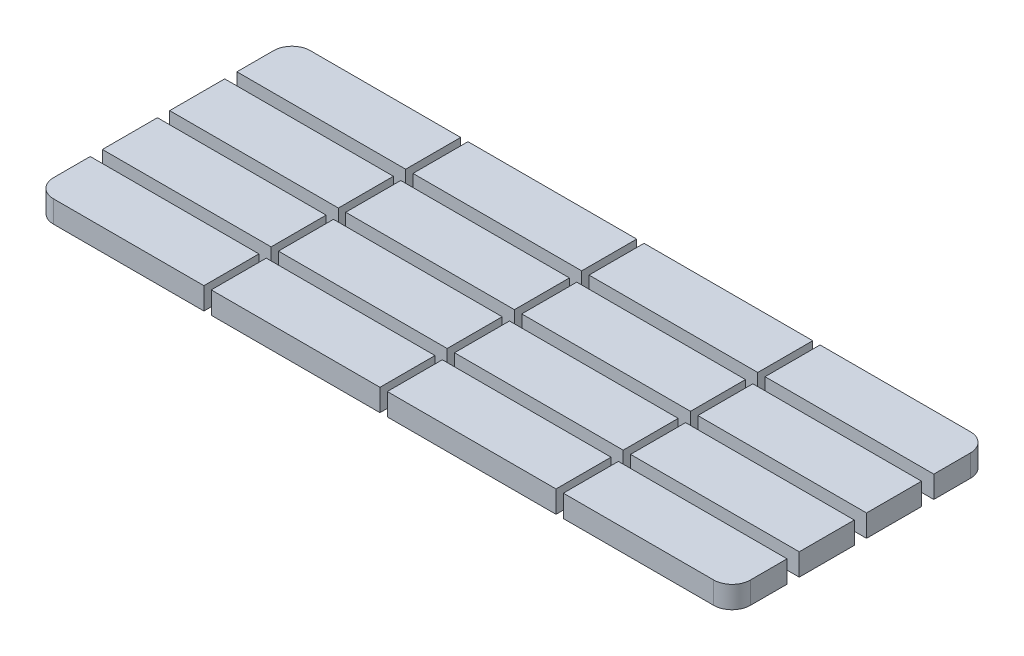
SolidWorks part; units mm, degrees
ref_plane "Front Plane" through (0, 0, 0) normal (0, 0, 1) x (1, 0, 0)
ref_plane "Top Plane" through (0, 0, 0) normal (0, 1, 0) x (1, 0, 0)
ref_plane "Right Plane" through (0, 0, 0) normal (1, 0, 0) x (0, 0, -1)
sketch "Sketch1" plane through (0, 0, 0) normal (0, 1, 0) x (1, 0, 0)
  line L0 (-57.3291, 9.17) -> (-34.3291, 9.17)
  line L1 (-54.8291, 19.17) -> (35.1709, 19.17)
  line L2 (-59.8291, 14.17) -> (-59.8291, -15.83)
  line L3 (-54.8291, -20.83) -> (35.1709, -20.83)
  line L4 (40.1709, 14.17) -> (40.1709, -15.83)
  line L5 (37.6709, 0) -> (14.6709, 0)
  line L6 (-57.3291, -10.83) -> (-34.3291, -10.83)
  line L7 (-33.3291, 16.67) -> (-33.3291, 9.17)
  line L8 (-9.3291, 16.67) -> (-9.3291, 9.17)
  line L9 (14.6709, 16.67) -> (14.6709, 9.17)
  line L10 (-34.3291, 16.67) -> (-34.3291, 9.17)
  line L11 (-54.8291, 16.67) -> (-34.3291, 16.67)
  line L12 (-57.3291, 14.17) -> (-57.3291, 9.17)
  line L13 (-54.8291, -18.33) -> (-34.3291, -18.33)
  line L14 (37.6709, 14.17) -> (37.6709, 9.17)
  line L15 (-10.3291, 16.67) -> (-10.3291, 9.17)
  line L16 (13.6709, 16.67) -> (13.6709, 9.17)
  line L17 (-33.3291, -18.33) -> (-10.3291, -18.33)
  line L18 (-33.3291, -10.83) -> (-10.3291, -10.83)
  line L19 (-34.3291, 0) -> (-57.3291, 0)
  line L20 (-33.3291, 9.17) -> (-10.3291, 9.17)
  line L21 (-33.3291, 16.67) -> (-10.3291, 16.67)
  line L22 (-9.3291, 16.67) -> (13.6709, 16.67)
  line L23 (-9.3291, 9.17) -> (13.6709, 9.17)
  line L24 (-10.3291, 0) -> (-33.3291, 0)
  line L25 (-9.3291, -10.83) -> (13.6709, -10.83)
  line L26 (-9.3291, -18.33) -> (13.6709, -18.33)
  line L27 (14.6709, -18.33) -> (35.1709, -18.33)
  line L28 (14.6709, -10.83) -> (37.6709, -10.83)
  line L29 (13.6709, 0) -> (-9.3291, 0)
  line L30 (14.6709, 16.67) -> (35.1709, 16.67)
  line L31 (14.6709, 9.17) -> (37.6709, 9.17)
  line L32 (-57.3291, 7.5) -> (-34.3291, 7.5)
  line L33 (-57.3291, -1.67) -> (-34.3291, -1.67)
  line L34 (-57.3291, -9.17) -> (-34.3291, -9.17)
  line L35 (-57.3291, 7.5) -> (-57.3291, 0)
  line L36 (-34.3291, 7.5) -> (-34.3291, 0)
  line L37 (-33.3291, 7.5) -> (-33.3291, 0)
  line L38 (-33.3291, 7.5) -> (-10.3291, 7.5)
  line L39 (-57.3291, -1.67) -> (-57.3291, -9.17)
  line L40 (-34.3291, -1.67) -> (-34.3291, -9.17)
  line L41 (-33.3291, -1.67) -> (-33.3291, -9.17)
  line L42 (-33.3291, -1.67) -> (-10.3291, -1.67)
  line L43 (-57.3291, -10.83) -> (-57.3291, -15.83)
  line L44 (-34.3291, -10.83) -> (-34.3291, -18.33)
  line L45 (-33.3291, -10.83) -> (-33.3291, -18.33)
  line L46 (-33.3291, -9.17) -> (-10.3291, -9.17)
  line L47 (-10.3291, 7.5) -> (-10.3291, 0)
  line L48 (-9.3291, 7.5) -> (-9.3291, 0)
  line L49 (-9.3291, 7.5) -> (13.6709, 7.5)
  line L50 (-10.3291, -1.67) -> (-10.3291, -9.17)
  line L51 (-9.3291, -1.67) -> (-9.3291, -9.17)
  line L52 (-9.3291, -1.67) -> (13.6709, -1.67)
  line L53 (-10.3291, -10.83) -> (-10.3291, -18.33)
  line L54 (-9.3291, -10.83) -> (-9.3291, -18.33)
  line L55 (-9.3291, -9.17) -> (13.6709, -9.17)
  line L56 (13.6709, -10.83) -> (13.6709, -18.33)
  line L57 (14.6709, -10.83) -> (14.6709, -18.33)
  line L58 (14.6709, -9.17) -> (37.6709, -9.17)
  line L59 (13.6709, -1.67) -> (13.6709, -9.17)
  line L60 (14.6709, -1.67) -> (14.6709, -9.17)
  line L61 (14.6709, -1.67) -> (37.6709, -1.67)
  line L62 (13.6709, 7.5) -> (13.6709, 0)
  line L63 (14.6709, 7.5) -> (14.6709, 0)
  line L64 (14.6709, 7.5) -> (37.6709, 7.5)
  line L65 (37.6709, 7.5) -> (37.6709, 0)
  line L66 (37.6709, -1.67) -> (37.6709, -9.17)
  line L67 (37.6709, -10.83) -> (37.6709, -15.83)
  line L68 (14.6709, -9.17) -> (37.6709, -9.17)
  arc A0 (35.1709, 19.17) -> (40.1709, 14.17) centre (35.1709, 14.17) cw
  arc A1 (35.1709, -20.83) -> (40.1709, -15.83) centre (35.1709, -15.83) ccw
  arc A2 (-59.8291, -15.83) -> (-54.8291, -20.83) centre (-54.8291, -15.83) ccw
  arc A3 (-54.8291, 19.17) -> (-59.8291, 14.17) centre (-54.8291, 14.17) ccw
  arc A4 (35.1709, -18.33) -> (37.6709, -15.83) centre (35.1709, -15.83) ccw
  arc A5 (35.1709, 16.67) -> (37.6709, 14.17) centre (35.1709, 14.17) cw
  arc A6 (-54.8291, 16.67) -> (-57.3291, 14.17) centre (-54.8291, 14.17) ccw
  arc A7 (-57.3291, -15.83) -> (-54.8291, -18.33) centre (-54.8291, -15.83) ccw
  point P8 (40.1709, -20.83)
  point P11 (-59.8291, -20.83)
  point P14 (-59.8291, 19.17)
  dimension "D3" = 5
  dimension "D8" = 7.5
  dimension "D1" = 40
  dimension "D2" = 100
  dimension "D4" = 10
  dimension "D5" = 2.5
  dimension "D6" = 2.5
  dimension "D7" = 2.5
  dimension "D11" = 35
  dimension "D13" = 1.67
  dimension "D16" = 23
extrude "Boss-Extrude1" add sketch "Sketch1" along normal blind 3 contours L11 A6 L12 L0 L10 | L36 L32 L35 L19 | L40 L33 L39 L34 | L43 A7 L13 L44 L6 | L53 L18 L45 L17 | L50 L42 L41 L46 | L47 L38 L37 L24 | L21 L7 L20 L15 | L8 L23 L16 L22 | L62 L49 L48 L29 | L56 L25 L54 L26 | L27 A4 L67 L28 L57 | L66 L61 L60 L58 | L65 L64 L63 L5 | L52 L59 L55 L51 | L31 L14 A5 L30 L9
